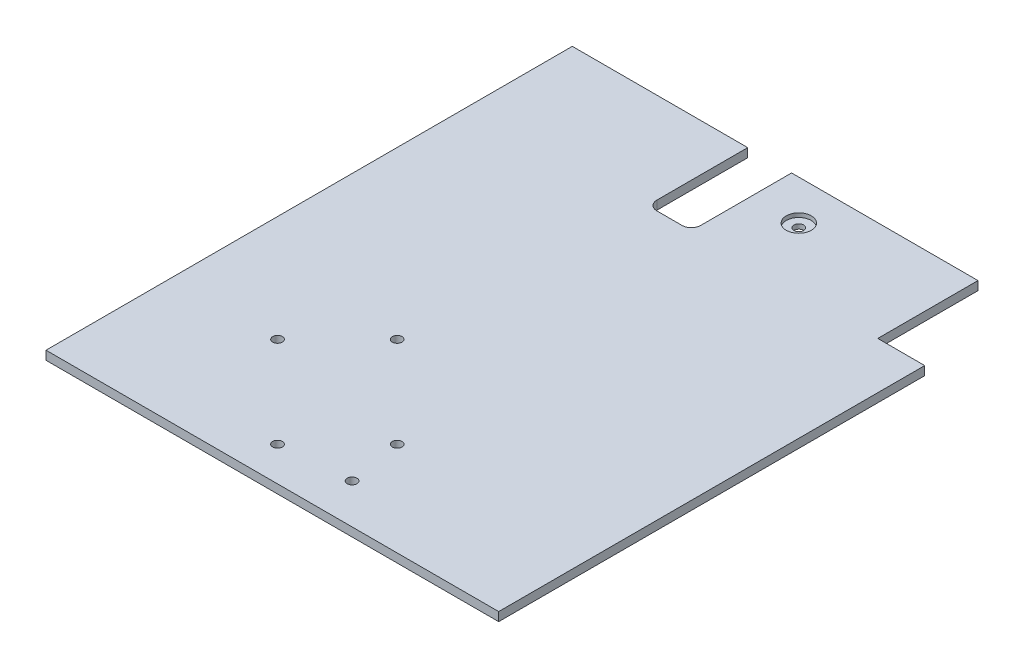
SolidWorks part; units mm, degrees
ref_plane "Front" through (0, 0, 0) normal (0, 0, 1) x (1, 0, 0)
ref_plane "Top" through (0, 0, 0) normal (0, 1, 0) x (1, 0, 0)
ref_plane "Right" through (0, 0, 0) normal (1, 0, 0) x (0, 0, -1)
sketch "Sketch1" plane through (0, 0, 0) normal (0, 1, 0) x (1, 0, 0)
  line L1 (-72.25, -84) -> (72.25, -84)
  line L2 (-72.25, -84) -> (-72.25, 84)
  line L3 (-72.25, 84) -> (72.25, 84)
  line L4 (72.25, -84) -> (72.25, 84)
  line L5 (-72.25, -84) -> (72.25, 84) construction
  line L6 (-72.25, 84) -> (72.25, -84) construction
  point P0 (0, 0)
  dimension "D1" = 168
  dimension "D2" = 144.5
extrude "Boss-Extrude1" add sketch "Sketch1" along normal blind 2.8
sketch "Sketch2" plane through (0, 2.8, 0) normal (0, 1, 0) x (1, 0, 0)
  line L0 (72.25, 84) -> (-72.25, 84) construction
  line L1 (57.25, 84) -> (72.25, 84)
  line L2 (57.25, 84) -> (57.25, 52)
  line L3 (57.25, 52) -> (72.25, 52)
  line L4 (72.25, 84) -> (72.25, 52)
  line L5 (57.25, 84) -> (72.25, 52) construction
  line L6 (57.25, 52) -> (72.25, 84) construction
  line L7 (72.25, -84) -> (72.25, 84) construction
  line L8 (-72.25, -84) -> (72.25, -84) construction
  line L9 (-38.2916, -44.0503) -> (-9.3003, -73.0416) construction
  line L10 (-38.2916, -44.0503) -> (-19.1997, -24.9584) construction
  line L11 (-19.1997, -24.9584) -> (9.7916, -53.9497) construction
  line L12 (-9.3003, -73.0416) -> (9.7916, -53.9497) construction
  line L13 (-38.2916, -44.0503) -> (9.7916, -53.9497) construction
  line L14 (-19.1997, -24.9584) -> (-9.3003, -73.0416) construction
  line L15 (-72.25, 84) -> (-72.25, -84) construction
  circle A0 centre (-19.1997, -24.9584) radius 1.55
  circle A1 centre (9.7916, -53.9497) radius 1.55
  circle A2 centre (-9.3003, -73.0416) radius 1.55
  circle A3 centre (-38.2916, -44.0503) radius 1.55
  point P4 (64.75, 68)
  point P13 (-14.25, -49)
  dimension "D6" = 3.1
  dimension "D7" = 3.1
  dimension "D8" = 3.1
  dimension "D9" = 3.1
  dimension "D1" = 15
  dimension "D2" = 32
  dimension "D3" = 27
  dimension "D4" = 41
  dimension "D5" = 45
  dimension "D10" = 58
  dimension "D11" = 35
extrude "Cut-Extrude1" cut sketch "Sketch2" against normal up to next
sketch "Sketch5" plane through (0, 2.8, 0) normal (0, 1, 0) x (1, 0, 0)
  line L0 (57.25, 84) -> (-72.25, 84) construction
  line L1 (-72.25, 84) -> (-72.25, -84) construction
  line L2 (-72.25, -84) -> (72.25, -84) construction
  circle A0 centre (12.75, 71.3) radius 1.55
  circle A1 centre (12.75, -71.3) radius 1.55
  dimension "D1" = 3.1
  dimension "D2" = 12.7
  dimension "D3" = 85
  dimension "D4" = 3.1
  dimension "D5" = 12.7
extrude "Cut-Extrude2" cut sketch "Sketch5" against normal up to next
sketch "Sketch6" plane through (0, 2.8, 0) normal (0, 1, 0) x (1, 0, 0)
  circle A0 centre (12.75, 71.3) radius 4
  dimension "D1" = 8
extrude "Cut-Extrude3" cut sketch "Sketch6" against normal blind 1.3
sketch "Sketch7" plane through (0, 2.8, 0) normal (0, 1, 0) x (1, 0, 0)
  line L0 (-16.25, 84) -> (-16.25, 55)
  line L1 (57.25, 84) -> (-72.25, 84) construction
  line L2 (-13.25, 52) -> (-5.25, 52)
  line L3 (-2.25, 55) -> (-2.25, 84)
  line L4 (-2.25, 84) -> (-16.25, 84)
  line L5 (-72.25, 84) -> (-72.25, -84) construction
  arc A2 (-2.25, 55) -> (-5.25, 52) centre (-5.25, 55) cw
  arc A3 (-13.25, 52) -> (-16.25, 55) centre (-13.25, 55) cw
  point P10 (-2.25, 52)
  point P13 (-16.25, 52)
  dimension "D2" = 56
  dimension "D3" = 14
  dimension "D4" = 3
  dimension "D1" = 32
extrude "Cut-Extrude4" cut sketch "Sketch7" against normal up to next
